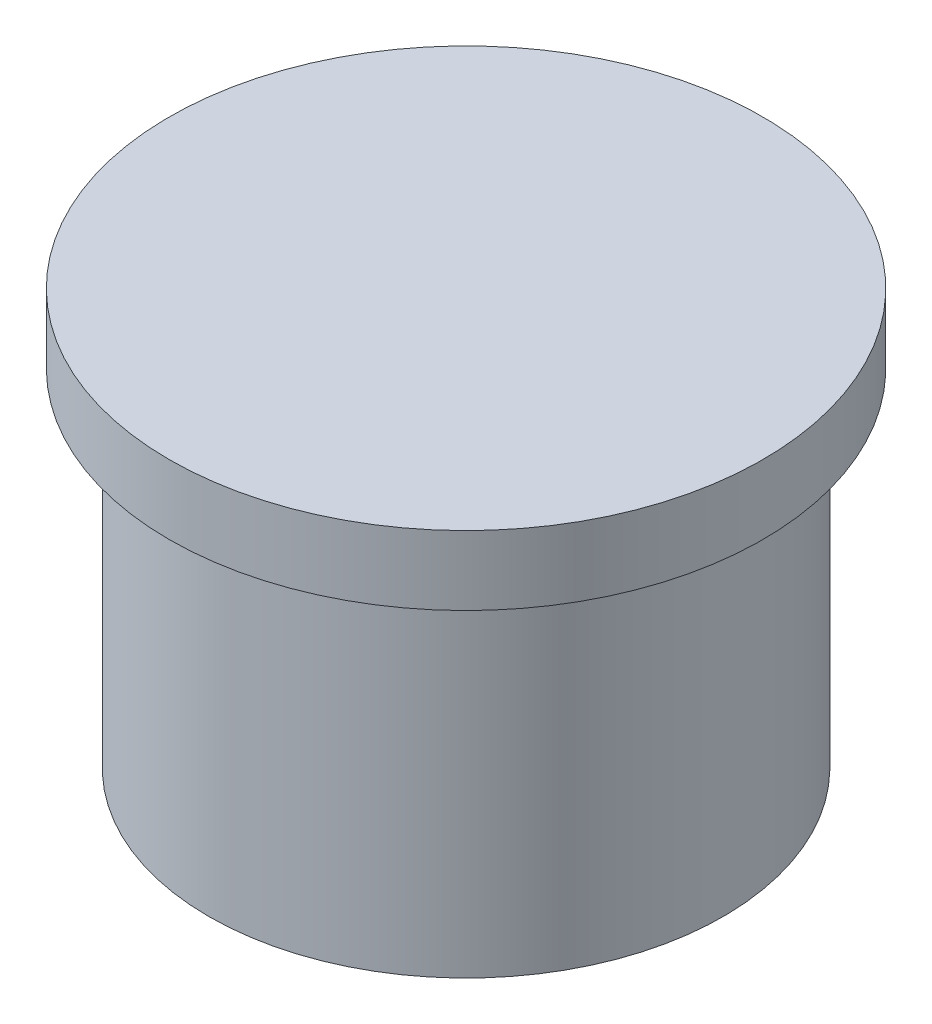
SolidWorks part; units mm, degrees
ref_plane "Piano frontale" through (0, 0, 0) normal (0, 0, 1) x (1, 0, 0)
ref_plane "Piano superiore" through (0, 0, 0) normal (0, 1, 0) x (1, 0, 0)
ref_plane "Piano destro" through (0, 0, 0) normal (1, 0, 0) x (0, 0, -1)
sketch "Schizzo1" plane through (0, 0, 0) normal (0, 1, 0) x (1, 0, 0)
  circle A0 centre (0, 0) radius 26
  dimension "D1" = 52
extrude "Estrusione-Estrusione1" add sketch "Schizzo1" along normal blind 35 contours A0
sketch "Schizzo2" plane through (0, 35, 0) normal (0, 1, 0) x (1, 0, 0)
  circle A0 centre (0, 0) radius 30
  dimension "D1" = 60
extrude "Estrusione-Estrusione2" add sketch "Schizzo2" along normal blind 7
